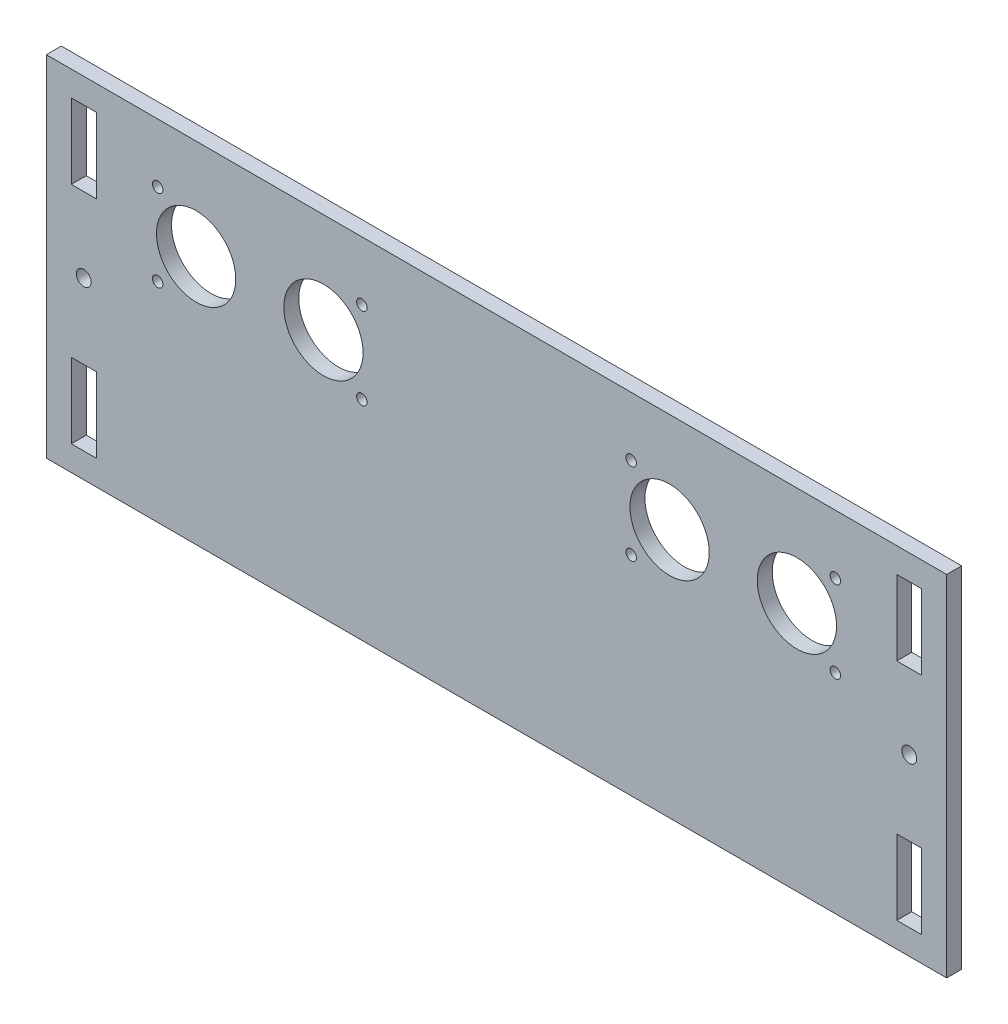
SolidWorks part; units mm, degrees
material "PMMA"
ref_plane "Front Plane" through (0, 0, 0) normal (0, 0, 1) x (1, 0, 0)
ref_plane "Top Plane" through (0, 0, 0) normal (0, 1, 0) x (1, 0, 0)
ref_plane "Right Plane" through (0, 0, 0) normal (1, 0, 0) x (0, 0, -1)
sketch "Schizzo1" plane through (0, 0, 0) normal (0, 0, 1) x (1, 0, 0)
  line L0 (90.17, 35) -> (-90.17, -35) construction
  line L1 (-90.17, 35) -> (90.17, 35)
  line L2 (-90.17, 35) -> (-90.17, -35)
  line L3 (-90.17, -35) -> (90.17, -35)
  line L4 (90.17, 35) -> (90.17, -35)
  point P4 (0, 0)
  dimension "D1" = 70
  dimension "D2" = 180.34
extrude "Estrusione-Estrusione1" add sketch "Schizzo1" along normal blind 3
sketch "Schizzo2" plane through (0, 0, 0) normal (0, 0, 1) x (1, 0, 0)
  line L0 (-90.17, 0) -> (90.17, 0) construction
  line L1 (-85.17, 30) -> (-80.17, 30)
  line L2 (-85.17, 30) -> (-85.17, 15)
  line L3 (-85.17, 15) -> (-80.17, 15)
  line L4 (-80.17, 30) -> (-80.17, 15)
  line L5 (-90.17, 35) -> (-90.17, -35) construction
  line L6 (90.17, -35) -> (90.17, 35) construction
  line L7 (0, 35) -> (0, -35) construction
  line L8 (90.17, 35) -> (-90.17, 35) construction
  line L9 (-90.17, -35) -> (90.17, -35) construction
  line L10 (-85.17, -30) -> (-85.17, -15)
  line L11 (-85.17, -15) -> (-80.17, -15)
  line L12 (-80.17, -30) -> (-80.17, -15)
  line L13 (-85.17, -30) -> (-80.17, -30)
  line L14 (85.17, 30) -> (85.17, 15)
  line L15 (85.17, 30) -> (80.17, 30)
  line L16 (80.17, 30) -> (80.17, 15)
  line L17 (85.17, 15) -> (80.17, 15)
  line L18 (85.17, -30) -> (85.17, -15)
  line L19 (85.17, -30) -> (80.17, -30)
  line L20 (80.17, -30) -> (80.17, -15)
  line L21 (85.17, -15) -> (80.17, -15)
  line L22 (-82.67, 15) -> (-82.67, -15) construction
  circle A0 centre (-82.67, 0) radius 1.5
  circle A1 centre (82.67, 0) radius 1.5
  dimension "D5" = 3
  dimension "D1" = 5
  dimension "D2" = 5
  dimension "D3" = 15
  dimension "D4" = 15
extrude "Taglio-Estrusione1" cut sketch "Schizzo2" along direction (0, 0, 1) on the side of the normal through all
sketch "Schizzo3" plane through (0, 0, 0) normal (0, 0, 1) x (1, 0, 0)
  line L0 (-60.17, 15) -> (-34.67, 15) construction
  line L1 (-90.17, -35) -> (90.17, -35) construction
  line L2 (-90.17, 35) -> (-90.17, -35) construction
  line L3 (0, 35) -> (0, -35) construction
  line L4 (90.17, 35) -> (-90.17, 35) construction
  line L5 (-47.42, 15) -> (-47.42, 10.25) construction
  line L6 (-69.92, 25.25) -> (-24.92, 25.25) construction
  line L7 (-69.92, 25.25) -> (-69.92, 4.75) construction
  line L8 (-69.92, 4.75) -> (-24.92, 4.75) construction
  line L9 (-24.92, 25.25) -> (-24.92, 4.75) construction
  circle A0 centre (-60.17, 15) radius 7.94
  circle A1 centre (-34.67, 15) radius 7.94
  circle A2 centre (60.17, 15) radius 7.94
  circle A3 centre (34.67, 15) radius 7.94
  circle A4 centre (-26.97, 6.8) radius 1.05
  circle A5 centre (-26.97, 23.2) radius 1.05
  circle A6 centre (-67.87, 6.8) radius 1.05
  circle A7 centre (-67.87, 23.2) radius 1.05
  circle A8 centre (26.97, 23.2) radius 1.05
  circle A9 centre (26.97, 6.8) radius 1.05
  circle A10 centre (67.87, 6.8) radius 1.05
  circle A11 centre (67.87, 23.2) radius 1.05
  point P20 (-24.92, 15)
  point P23 (-47.42, 25.25)
  dimension "D2" = 15.88
  dimension "D5" = 45
  dimension "D7" = 2.1
  dimension "D1" = 25.5
  dimension "D3" = 50
  dimension "D4" = 30
  dimension "D6" = 20.5
  dimension "D8" = 2.05
  dimension "D9" = 2.05
extrude "Taglio-Estrusione2" cut sketch "Schizzo3" along direction (0, 0, 1) on the side of the normal through all
equation "\"Thickness3\"= 3"
equation "\"D1@Estrusione-Estrusione1\"=\"Thickness3\""
equation "\"Thickness5\"= 5"
equation "\"D1@Schizzo2\"=\"Thickness5\""
equation "\"D2@Schizzo2\"=\"Thickness5\""
